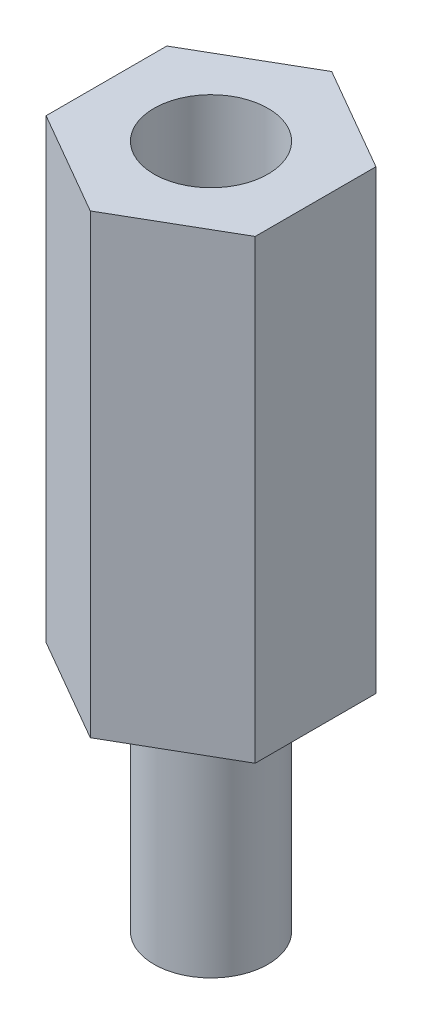
SolidWorks part; units mm, degrees
ref_plane "Alzado" through (0, 0, 0) normal (0, 0, 1) x (1, 0, 0)
ref_plane "Planta" through (0, 0, 0) normal (0, 1, 0) x (1, 0, 0)
ref_plane "Vista lateral" through (0, 0, 0) normal (1, 0, 0) x (0, 0, -1)
sketch "Croquis1" plane through (0, 0, 0) normal (0, 1, 0) x (1, 0, 0)
  line L1 (0, 3.1754) -> (-2.75, 1.5877)
  line L2 (-2.75, 1.5877) -> (-2.75, -1.5877)
  line L3 (-2.75, -1.5877) -> (0, -3.1754)
  line L4 (0, -3.1754) -> (2.75, -1.5877)
  line L5 (2.75, -1.5877) -> (2.75, 1.5877)
  line L6 (2.75, 1.5877) -> (0, 3.1754)
  circle A0 centre (0, 0) radius 2.75 construction
  dimension "D1" = 5.5
extrude "Saliente-Extruir1" add sketch "Croquis1" along normal blind 12
sketch "Croquis2" plane through (0, 0, 0) normal (0, -1, 0) x (1, 0, 0)
  circle A0 centre (0, 0) radius 1.5
  dimension "D1" = 3
extrude "Saliente-Extruir2" add sketch "Croquis2" along normal blind 6
sketch "Croquis3" plane through (0, 12, 0) normal (0, 1, 0) x (1, 0, 0)
  circle A0 centre (0, 0) radius 1.5
  dimension "D1" = 3
extrude "Cortar-Extruir1" cut sketch "Croquis3" against normal blind 6
